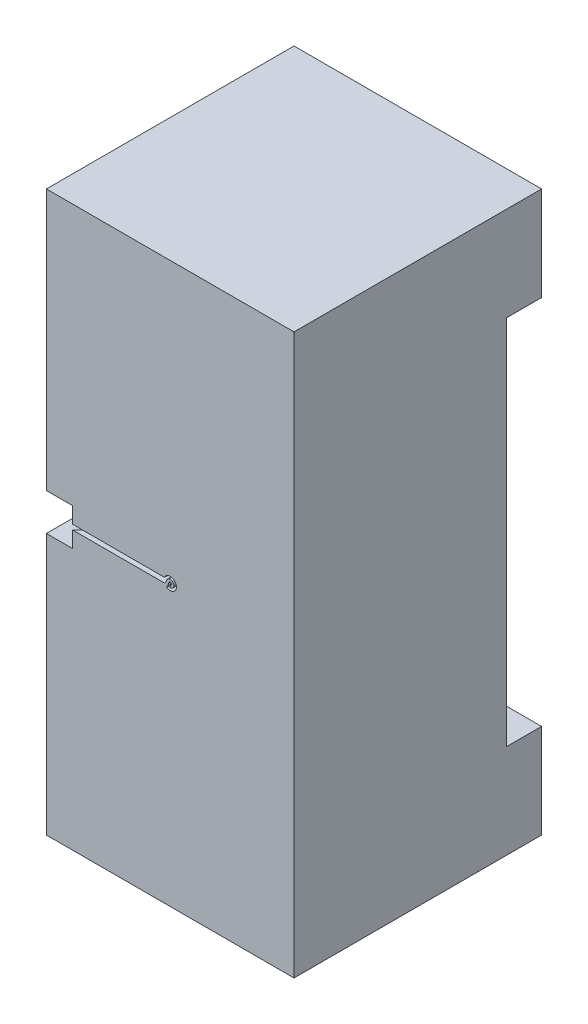
SolidWorks part; units mm, degrees
other "Markup1"
sketch "Sketch4" plane through (-50, 0, 50.1) normal (-0.123, -0.9831, 0.136) x (-0.0115, 0.1384, 0.9903)
ref_plane "Alzado" through (0, 0, 0) normal (0, 0, 1) x (1, 0, 0)
ref_plane "Planta" through (0, 0, 0) normal (0, 1, 0) x (1, 0, 0)
ref_plane "Vista lateral" through (0, 0, 0) normal (1, 0, 0) x (0, 0, -1)
sketch "Sketch1" plane through (0, 0, 0) normal (0, 1, 0) x (1, 0, 0)
  line L1 (-50, 50) -> (50, 50)
  line L2 (-50, 50) -> (-50, -50)
  line L3 (-50, -50) -> (50, -50)
  line L4 (50, 50) -> (50, -50)
  line L5 (-50, 50) -> (50, -50) construction
  line L6 (-50, -50) -> (50, 50) construction
  point P0 (0, 0)
  dimension "D1" = 100
  dimension "D2" = 100
extrude "Boss-Extrude1" add sketch "Sketch1" along normal blind 226
sketch "Sketch2" plane through (0, 0, 50) normal (0, 0, 1) x (1, 0, 0)
  line L0 (-50, 226) -> (-50, 0) construction
  circle A0 centre (0, 113) radius 5
  point P4 (-50, 113)
  dimension "D1" = 10
ref_plane "Plane1" through (0, 0, 0) normal (0.7071, 0, 0.7071) x (0.7071, 0, -0.7071)
ref_plane "Plane2" through (50, 0, -50) normal (-0.7071, 0, 0.7071) x (0, -1, 0)
sketch "Sketch5" plane through (50, 0, -50) normal (-0.7071, 0, 0.7071) x (0, -1, 0)
  line L1 (-38, 10) -> (-188, 10)
  line L2 (-38, 10) -> (-38, -10)
  line L3 (-38, -10) -> (-188, -10)
  line L4 (0, 0) -> (0, 70.7107)
  line L5 (-226, 0) -> (0, 0)
  line L6 (-226, 70.7107) -> (-226, 0)
  line L7 (0, 70.7107) -> (-226, 70.7107)
  line L8 (0, 0) -> (0, 70.7107)
  line L9 (-226, 0) -> (0, 0)
  line L10 (-226, 70.7107) -> (-226, 0)
  line L11 (0, 70.7107) -> (-226, 70.7107)
  line L12 (-188, 10) -> (-188, -10)
  line L13 (-38, 10) -> (-188, -10) construction
  line L14 (-38, -10) -> (-188, 10) construction
  point P2 (-113, 0)
  dimension "D2" = 20
  dimension "D3" = 150
  dimension "D1" = 0
extrude "Cut-Extrude2" cut sketch "Sketch5" along normal blind 125 contours L9 L12 L3 L2 | L1 L12 L9 L2
ref_plane "Plane3" through (-50, 0, 50) normal (-0.7071, 0, 0.7071) x (0.7071, 0, 0.7071)
sketch "Sketch6" plane through (-50, 0, 50) normal (-0.7071, 0, 0.7071) x (0.7071, 0, 0.7071)
  line L0 (0, 226) -> (0, 0) construction
  line L1 (7.5, 120.5) -> (-7.5, 120.5)
  line L2 (7.5, 120.5) -> (7.5, 105.5)
  line L3 (7.5, 105.5) -> (-7.5, 105.5)
  line L4 (-7.5, 120.5) -> (-7.5, 105.5)
  line L5 (7.5, 120.5) -> (-7.5, 105.5) construction
  line L6 (7.5, 105.5) -> (-7.5, 120.5) construction
  point P0 (0, 113)
  dimension "D1" = 15
  dimension "D2" = 15
extrude "Cut-Extrude3" cut sketch "Sketch6" against normal blind 125
sketch "Sketch8" plane through (0, 0, 50) normal (0, 0, 1) x (1, 0, 0)
  line L0 (-39.3934, 113) -> (-5, 113) construction
  line L1 (-39.3934, 120.5) -> (-39.3934, 105.5) construction
  line L2 (-5, 113) -> (0, 113) construction
  line L3 (-39.3934, 112) -> (-5, 112)
  line L4 (-5, 112) -> (-2.2913, 112)
  line L5 (-39.3934, 114) -> (-5, 114)
  line L6 (-5, 114) -> (-2.2913, 114)
  line L7 (-39.3934, 120.5) -> (-39.3934, 105.5)
  line L8 (-5, 114) -> (0, 114) construction
  line L9 (-5, 112) -> (0, 112) construction
  circle A0 centre (0, 113) radius 5 construction
  arc A2 (-2.2913, 112) -> (-2.2913, 114) centre (0, 113) ccw
  line M5 (-39.3934, 120.5) -> (-39.3934, 105.5)
  dimension "D1" = 1
  dimension "D2" = 1
extrude "Cut-Extrude6" cut sketch "Sketch8" against normal blind 7.5 contours L4 A2 L6 L5 L3 M5
sketch "Sketch10" plane through (0, 0, 50) normal (0, 0, 1) x (1, 0, 0)
  line L2 (0, 112.5) -> (0, 111.5)
  line L3 (-28.3579, 112) -> (-2.2913, 112)
  line L4 (-2.2913, 114) -> (-28.3579, 114)
  line L5 (-28.3579, 114) -> (-28.3579, 112)
  arc A0 (-2.2913, 112) -> (-2.2913, 114) centre (0, 113) ccw
  arc A1 (-2.2913, 112) -> (-2.2913, 114) centre (0, 113) ccw
  arc A2 (-2.2913, 112) -> (-2.2913, 114) centre (0, 113) ccw
  arc A3 (0, 111.5) -> (-1.4184, 113.488) centre (0, 113) ccw
  circle A4 centre (0, 113) radius 1.5 construction
  circle A5 centre (0, 113) radius 2.5 construction
  arc A6 (0, 111.5) -> (-1.4184, 113.488) centre (0, 113) ccw
  arc A7 (0, 112.5) -> (-0.4728, 113.1627) centre (0, 113) ccw
  arc A8 (-1.4184, 113.488) -> (-2.2913, 112) centre (-5.5401, 114.9059) cw
  arc A9 (-0.4728, 113.1627) -> (-1.4184, 110.9413) centre (-16.533, 118.6875) cw
  dimension "D1" = 0
  dimension "D2" = 1
  dimension "D3" = 1
extrude "Boss-Extrude2" add sketch "Sketch10" against normal offset from surface (6.5 mm away) 1 contours A9 A7 L2 A3 A8 A2 up to face at (-14.1268, 113, 42.5)
